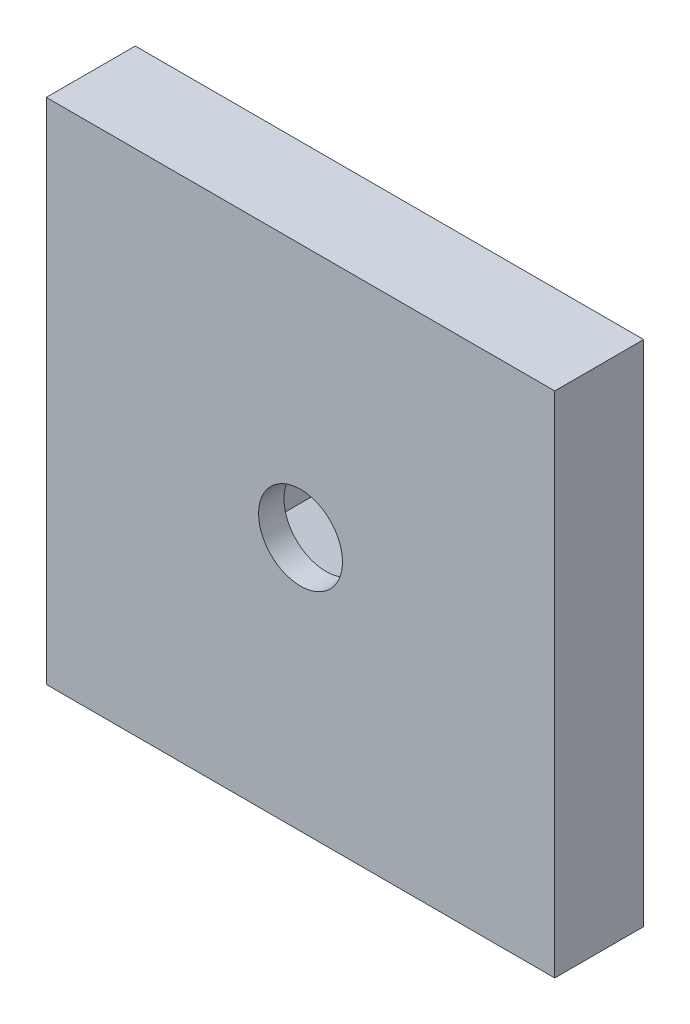
SolidWorks part; units mm, degrees
ref_plane "Front Plane" through (0, 0, 0) normal (0, 0, 1) x (1, 0, 0)
ref_plane "Top Plane" through (0, 0, 0) normal (0, 1, 0) x (1, 0, 0)
ref_plane "Right Plane" through (0, 0, 0) normal (1, 0, 0) x (0, 0, -1)
sketch "Sketch1" plane through (0, 0, 0) normal (0, 0, 1) x (1, 0, 0)
  line L1 (0, -3.2101) -> (2.78, -1.605)
  line L2 (2.78, -1.605) -> (2.78, 1.605)
  line L3 (2.78, 1.605) -> (0, 3.2101)
  line L4 (0, 3.2101) -> (-2.78, 1.605)
  line L5 (-2.78, 1.605) -> (-2.78, -1.605)
  line L6 (-2.78, -1.605) -> (0, -3.2101)
  line L7 (-10, 10) -> (10, 10)
  line L8 (-10, 10) -> (-10, -10)
  line L9 (-10, -10) -> (10, -10)
  line L10 (10, 10) -> (10, -10)
  line L11 (-10, 10) -> (10, -10) construction
  line L12 (-10, -10) -> (10, 10) construction
  circle A0 centre (0, 0) radius 2.78 construction
  dimension "D1" = 5.56
  dimension "D2" = 20
  dimension "D3" = 20
extrude "Boss-Extrude1" add sketch "Sketch1" along normal blind 2.5
sketch "Sketch2" plane through (0, 0, 2.5) normal (0, 0, 1) x (1, 0, 0)
  line L4 (10, -10) -> (10, 10)
  line L5 (10, 10) -> (-10, 10)
  line L6 (-10, 10) -> (-10, -10)
  line L7 (-10, -10) -> (10, -10)
  line L8 (10, -10) -> (10, 10)
  line L9 (10, 10) -> (-10, 10)
  line L10 (-10, 10) -> (-10, -10)
  line L11 (-10, -10) -> (10, -10)
  dimension "D1" = 0
extrude "Boss-Extrude2" add sketch "Sketch2" along normal blind 1
sketch "Sketch3" plane through (0, 0, 0) normal (0, 0, -1) x (-1, 0, 0)
  line L4 (-10, 10) -> (-10, -10)
  line L5 (-10, -10) -> (10, -10)
  line L6 (10, -10) -> (10, 10)
  line L7 (10, 10) -> (-10, 10)
  line L8 (-10, 10) -> (-10, -10)
  line L9 (-10, -10) -> (10, -10)
  line L10 (10, -10) -> (10, 10)
  line L11 (10, 10) -> (-10, 10)
  circle A0 centre (0, 0) radius 1.65
  dimension "D2" = 3.3
  dimension "D1" = 0
extrude "Cut-Extrude1" cut sketch "Sketch3" against normal through all contours A0
